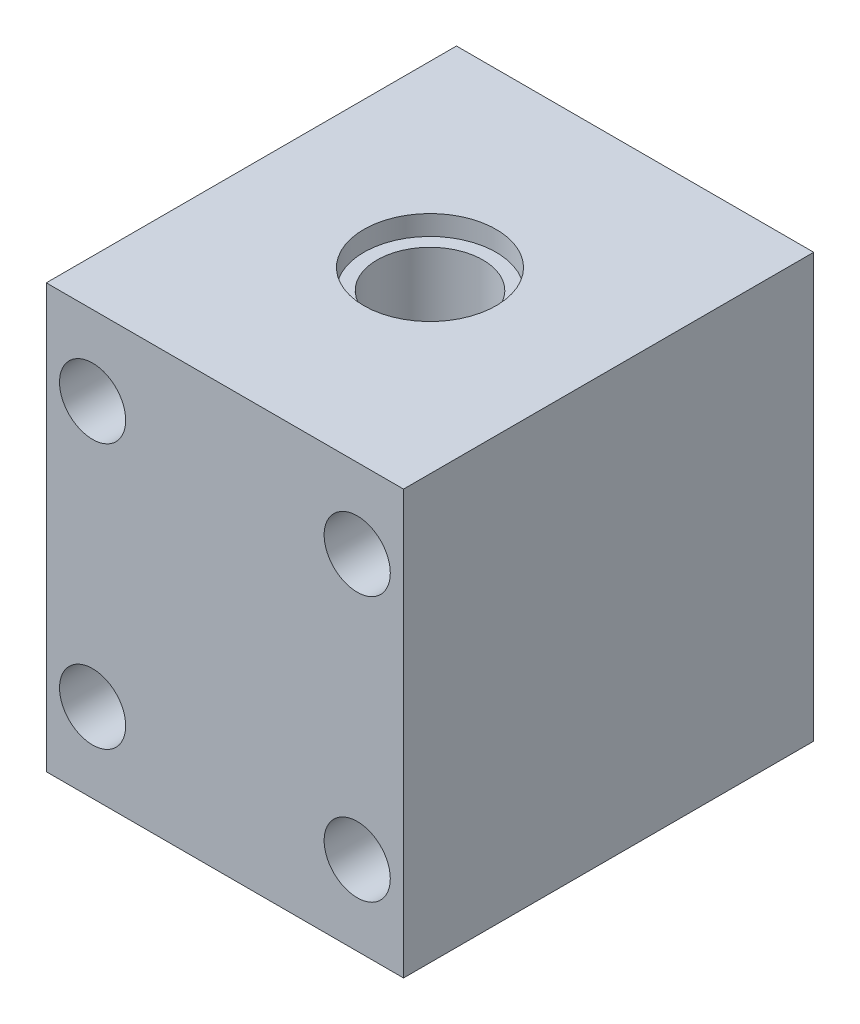
SolidWorks part; units mm, degrees
ref_plane "Piano frontale" through (0, 0, 0) normal (0, 0, 1) x (1, 0, 0)
ref_plane "Piano superiore" through (0, 0, 0) normal (0, 1, 0) x (1, 0, 0)
ref_plane "Piano destro" through (0, 0, 0) normal (1, 0, 0) x (0, 0, -1)
sketch "Schizzo1" plane through (0, 0, 0) normal (0, 0, 1) x (1, 0, 0)
  line L1 (-13.5, 16) -> (13.5, 16)
  line L2 (-13.5, 16) -> (-13.5, -16)
  line L3 (-13.5, -16) -> (13.5, -16)
  line L4 (13.5, 16) -> (13.5, -16)
  line L5 (-13.5, 16) -> (13.5, -16) construction
  line L6 (-13.5, -16) -> (13.5, 16) construction
  point P0 (0, 0)
  dimension "D1" = 27
  dimension "D2" = 32
extrude "Estrusione-Estrusione1" add sketch "Schizzo1" along normal blind 31
sketch "Schizzo2" plane through (0, 0, 0) normal (0, 0, -1) x (-1, 0, 0)
  line L1 (-10, 10) -> (10, 10) construction
  line L2 (-10, 10) -> (-10, -10) construction
  line L3 (-10, -10) -> (10, -10) construction
  line L4 (10, 10) -> (10, -10) construction
  line L5 (-10, 10) -> (10, -10) construction
  line L6 (-10, -10) -> (10, 10) construction
  circle A0 centre (-10, 10) radius 1.5
  circle A1 centre (10, 10) radius 1.5
  circle A2 centre (10, -10) radius 1.5
  circle A3 centre (-10, -10) radius 1.5
  point P0 (0, 0)
  dimension "D3" = 3
  dimension "D1" = 20
  dimension "D2" = 20
extrude "Taglio-Estrusione1" cut sketch "Schizzo2" against normal through all
sketch "Schizzo3" plane through (0, 16, 0) normal (0, 1, 0) x (1, 0, 0)
  line L1 (-13.5, 0) -> (13.5, -31) construction
  line L2 (13.5, 0) -> (-13.5, -31) construction
  circle A0 centre (0, -15.5) radius 4
  point P4 (0, 0)
  point P11 (0, -15.5)
  dimension "D1" = 8
extrude "Taglio-Estrusione2" cut sketch "Schizzo3" against normal through all
sketch "Schizzo4" plane through (0, 16, 0) normal (0, 1, 0) x (1, 0, 0)
  circle A0 centre (0, -15.5) radius 5
  circle A1 centre (0, -15.5) radius 4 construction
  dimension "D1" = 10
extrude "Taglio-Estrusione5" cut sketch "Schizzo4" against normal blind 1.5
sketch "Schizzo5" plane through (0, -16, 0) normal (0, -1, 0) x (1, 0, 0)
  circle A0 centre (0, 15.5) radius 5
  circle A1 centre (0, 15.5) radius 4 construction
  dimension "D1" = 10
extrude "Taglio-Estrusione6" cut sketch "Schizzo5" against normal blind 1.5
sketch "Schizzo6" plane through (0, 0, 31) normal (0, 0, 1) x (1, 0, 0)
  line L1 (-10, 10) -> (10, 10) construction
  line L2 (-10, 10) -> (-10, -10) construction
  line L3 (-10, -10) -> (10, -10) construction
  line L4 (10, 10) -> (10, -10) construction
  line L5 (-10, 10) -> (10, -10) construction
  line L6 (-10, -10) -> (10, 10) construction
  circle A0 centre (-10, 10) radius 2.5
  circle A1 centre (10, 10) radius 2.5
  circle A2 centre (10, -10) radius 2.5
  circle A3 centre (-10, -10) radius 2.5
  point P0 (0, 0)
  dimension "D1" = 5
extrude "Taglio-Estrusione7" cut sketch "Schizzo6" against normal blind 15
sketch "Schizzo7" plane through (0, 0, 31) normal (0, 0, 1) x (1, 0, 0)
  line L0 (-13.5, 16) -> (-13.5, -16) construction
  line L1 (-5.5, 6) -> (5.5, 6) construction
  line L2 (-5.5, 6) -> (-5.5, -6) construction
  line L3 (-5.5, -6) -> (5.5, -6) construction
  line L4 (5.5, 6) -> (5.5, -6) construction
  line L5 (-5.5, 6) -> (5.5, -6) construction
  line L6 (-5.5, -6) -> (5.5, 6) construction
  line L9 (-13.5, -16) -> (13.5, -16) construction
  circle A0 centre (-5.5, 6) radius 2.5
  circle A1 centre (5.5, 6) radius 2.5
  circle A2 centre (0, 0) radius 2.5
  circle A3 centre (5.5, -6) radius 2.5
  circle A4 centre (-5.5, -6) radius 2.5
  point P0 (0, 0)
  dimension "D3" = 5
  dimension "D1" = 8
  dimension "D2" = 10
